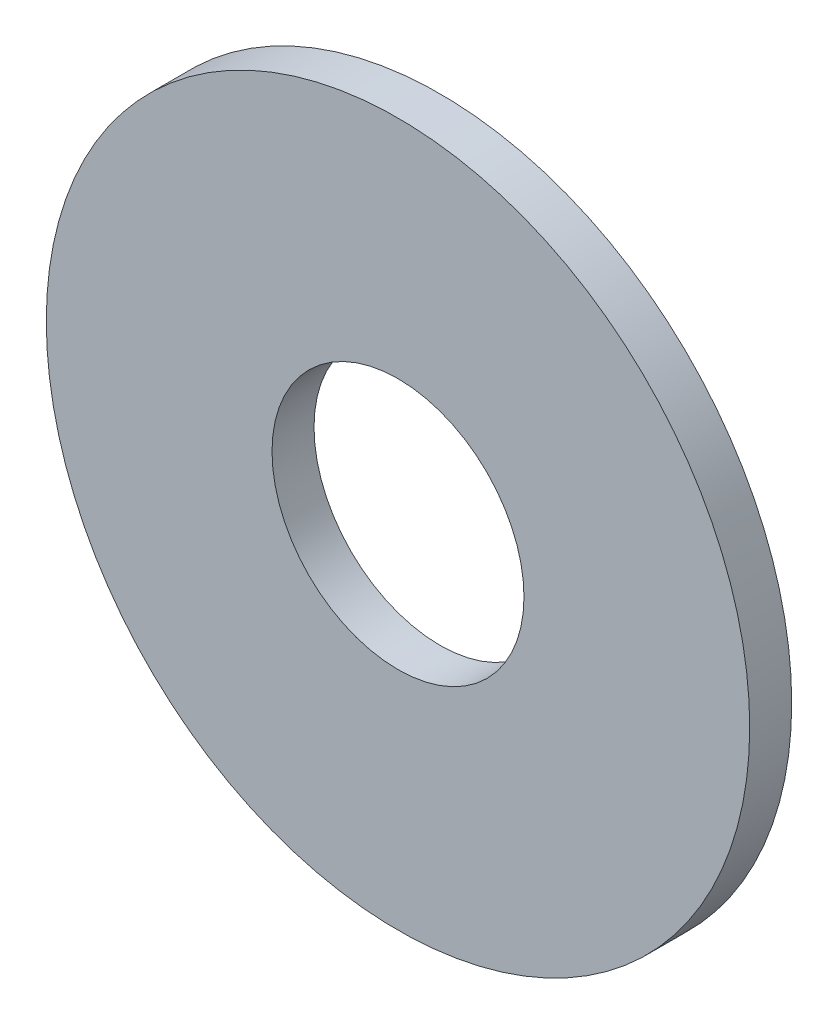
SolidWorks part; units mm, degrees
ref_plane "Plan1" through (0, 0, 0) normal (0, 0, 1) x (1, 0, 0)
ref_plane "Plan2" through (0, 0, 0) normal (0, 1, 0) x (1, 0, 0)
ref_plane "Plan3" through (0, 0, 0) normal (1, 0, 0) x (0, 0, -1)
sketch "Esquisse1" plane through (0, 0, 0) normal (0, 0, 1) x (1, 0, 0)
  circle A0 centre (0, 0) radius 16.75
  circle A1 centre (0, 0) radius 6
  dimension "D1" = 33.5
  dimension "D2" = 12
extrude "Base-Extrusion" add sketch "Esquisse1" along normal blind 2
